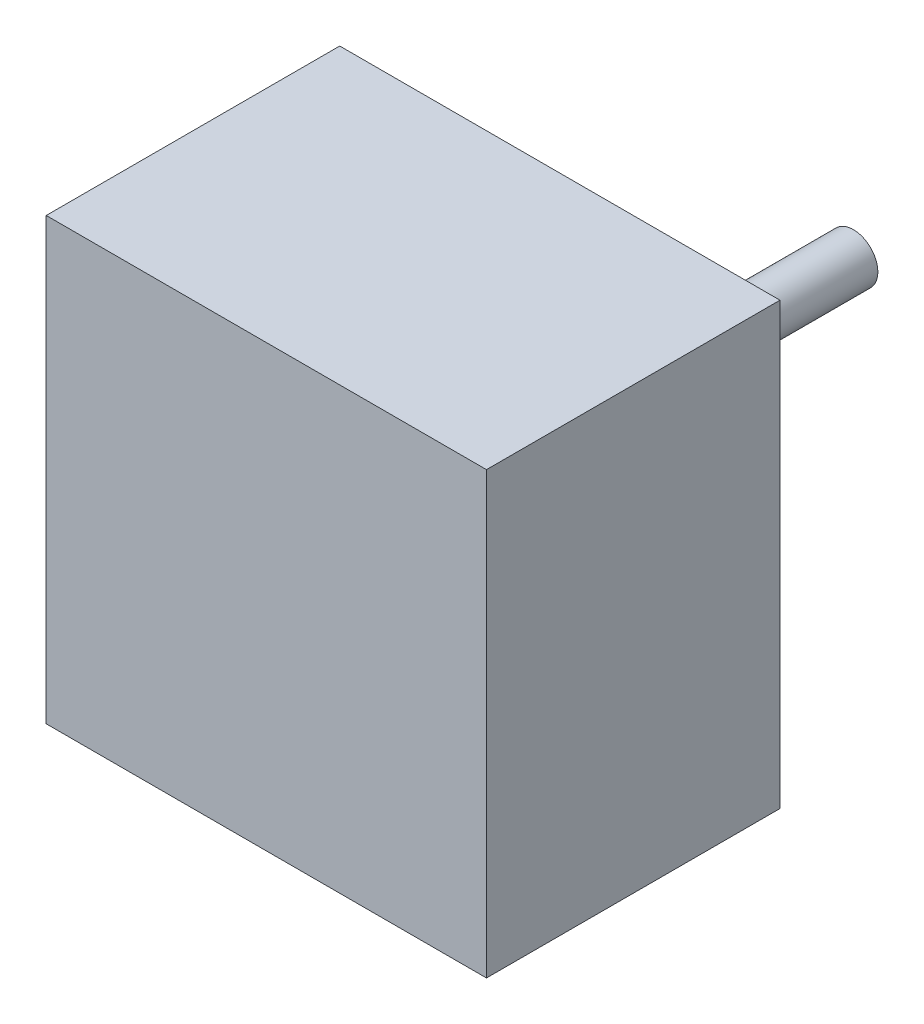
SolidWorks part; units mm, degrees
ref_plane "Front Plane" through (0, 0, 0) normal (0, 0, 1) x (1, 0, 0)
ref_plane "Top Plane" through (0, 0, 0) normal (0, 1, 0) x (1, 0, 0)
ref_plane "Right Plane" through (0, 0, 0) normal (1, 0, 0) x (0, 0, -1)
sketch "Sketch1" plane through (0, 0, 0) normal (0, 0, 1) x (1, 0, 0)
  circle A0 centre (0, 0) radius 12.5
  dimension "D1" = 25
extrude "Boss-Extrude1" add sketch "Sketch1" along normal blind 10
sketch "Sketch2" plane through (0, 0, 10) normal (0, 0, 1) x (1, 0, 0)
  line L1 (-22.5, 22.5) -> (22.5, 22.5)
  line L2 (-22.5, 22.5) -> (-22.5, -22.5)
  line L3 (-22.5, -22.5) -> (22.5, -22.5)
  line L4 (22.5, 22.5) -> (22.5, -22.5)
  line L5 (-22.5, 22.5) -> (22.5, -22.5) construction
  line L6 (-22.5, -22.5) -> (22.5, 22.5) construction
  point P0 (0, 0)
  dimension "D1" = 45
  dimension "D2" = 45
extrude "Boss-Extrude2" add sketch "Sketch2" along normal blind 30
sketch "Sketch4" plane through (0, 0, 0) normal (0, 0, -1) x (-1, 0, 0)
  circle A0 centre (0, 0) radius 2.5
extrude "Boss-Extrude3" add sketch "Sketch4" along normal blind 20
